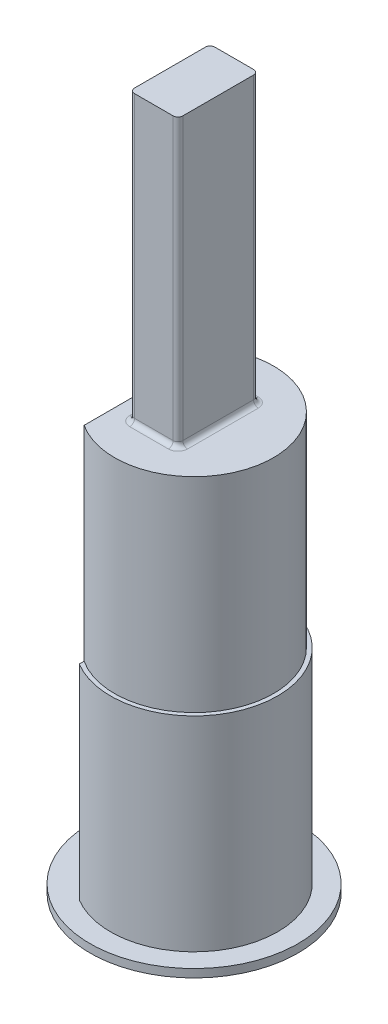
SolidWorks part; units mm, degrees
ref_plane "Front Plane" through (0, 0, 0) normal (0, 0, 1) x (1, 0, 0)
ref_plane "Top Plane" through (0, 0, 0) normal (0, 1, 0) x (1, 0, 0)
ref_plane "Right Plane" through (0, 0, 0) normal (1, 0, 0) x (0, 0, -1)
sketch "Sketch1" plane through (0, 0, 0) normal (0, 1, 0) x (1, 0, 0)
  line L0 (-2.69, 4.445) -> (-2.69, -4.445)
  arc A0 (-2.69, -4.445) -> (-2.69, 4.445) centre (0, 0) ccw
  dimension "D1" = 10.3911
  dimension "D2" = 8.89
extrude "Boss-Extrude1" add sketch "Sketch1" along normal blind 25.4
sketch "Sketch2" plane through (0, 25.4, 0) normal (0, 1, 0) x (1, 0, 0)
  line L1 (-1.2, -2.5) -> (1.2, -2.5)
  line L2 (-1.5, -2.2) -> (-1.5, 2.2)
  line L3 (-1.2, 2.5) -> (1.2, 2.5)
  line L4 (1.5, -2.2) -> (1.5, 2.2)
  line L5 (-1.5, -2.5) -> (1.5, 2.5) construction
  line L6 (-1.5, 2.5) -> (1.5, -2.5) construction
  arc A0 (-1.2, -2.5) -> (-1.5, -2.2) centre (-1.2, -2.2) cw
  arc A1 (1.2, -2.5) -> (1.5, -2.2) centre (1.2, -2.2) ccw
  arc A2 (1.2, 2.5) -> (1.5, 2.2) centre (1.2, 2.2) cw
  arc A3 (-1.5, 2.2) -> (-1.2, 2.5) centre (-1.2, 2.2) cw
  point P0 (0, 0)
  dimension "D3" = 0.3
  dimension "D1" = 5
  dimension "D2" = 3
extrude "Boss-Extrude2" add sketch "Sketch2" along normal blind 17.78
fillet "Fillet1" radius 0.3 8 edges at (1.4121, 25.4, 2.4121) (0, 25.4, 2.5) (-1.4121, 25.4, 2.4121) (-1.5, 25.4, 0) (-1.4121, 25.4, -2.4121) (0, 25.4, -2.5) (1.4121, 25.4, -2.4121) (1.5, 25.4, 0)
sketch "Sketch3" plane through (0, 0, 0) normal (0, -1, 0) x (1, 0, 0)
  circle A0 centre (0, 0) radius 6.4656
  arc A1 (-2.69, -4.445) -> (-2.69, 4.445) centre (0, 0) ccw construction
  dimension "D1" = 1.27
extrude "Boss-Extrude3" add sketch "Sketch3" along normal blind 0.508
sketch "Sketch4" plane through (0, 25.4, 0) normal (0, 1, 0) x (1, 0, 0)
  circle A0 centre (0, 0) radius 4.9416
  arc A1 (-2.69, -4.445) -> (-2.69, 4.445) centre (0, 0) ccw construction
  dimension "D1" = 0.254
extrude "Cut-Extrude1" cut sketch "Sketch4" against normal blind 12.7 flip side to cut
